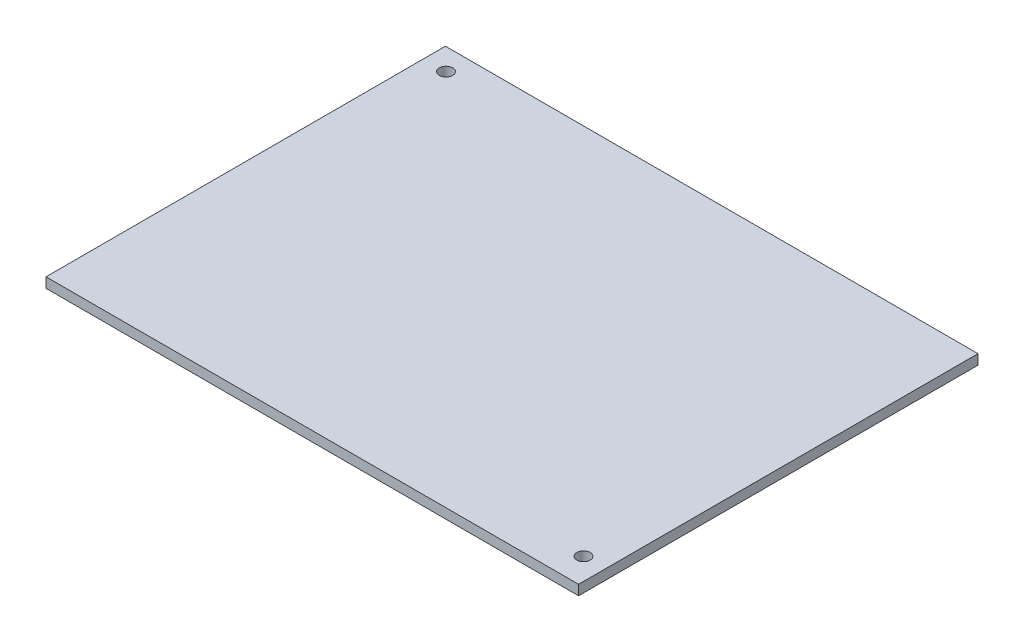
SolidWorks part; units mm, degrees
ref_plane "Plan de face" through (0, 0, 0) normal (0, 0, 1) x (1, 0, 0)
ref_plane "Plan de dessus" through (0, 0, 0) normal (0, 1, 0) x (1, 0, 0)
ref_plane "Plan de droite" through (0, 0, 0) normal (1, 0, 0) x (0, 0, -1)
sketch "Esquisse1" plane through (0, 0, 0) normal (0, 1, 0) x (1, 0, 0)
  line L1 (80, 60) -> (0, 60)
  line L2 (80, 60) -> (80, 0)
  line L3 (80, 0) -> (0, 0)
  line L4 (0, 60) -> (0, 0)
  dimension "D1" = 60
  dimension "D2" = 80
extrude "Boss.-Extru.1" add sketch "Esquisse1" along normal blind 1.5
sketch "Esquisse2" plane through (0, 1.5, 0) normal (0, 1, 0) x (1, 0, 0)
  line L0 (115.1447, 259.5) -> (575.8114, 259.5) construction
sketch "Esquisse3" plane through (0, 1.5, 0) normal (0, 1, 0) x (1, 0, 0)
  circle A0 centre (3.3553, 56.7338) radius 1
  circle A1 centre (76.7275, 4.0121) radius 1
  dimension "D1" = 2
extrude "Enlèv. mat.-Extru.1" cut sketch "Esquisse3" against normal up to surface (1.5 mm away) up to face at (40, 0, -30)
